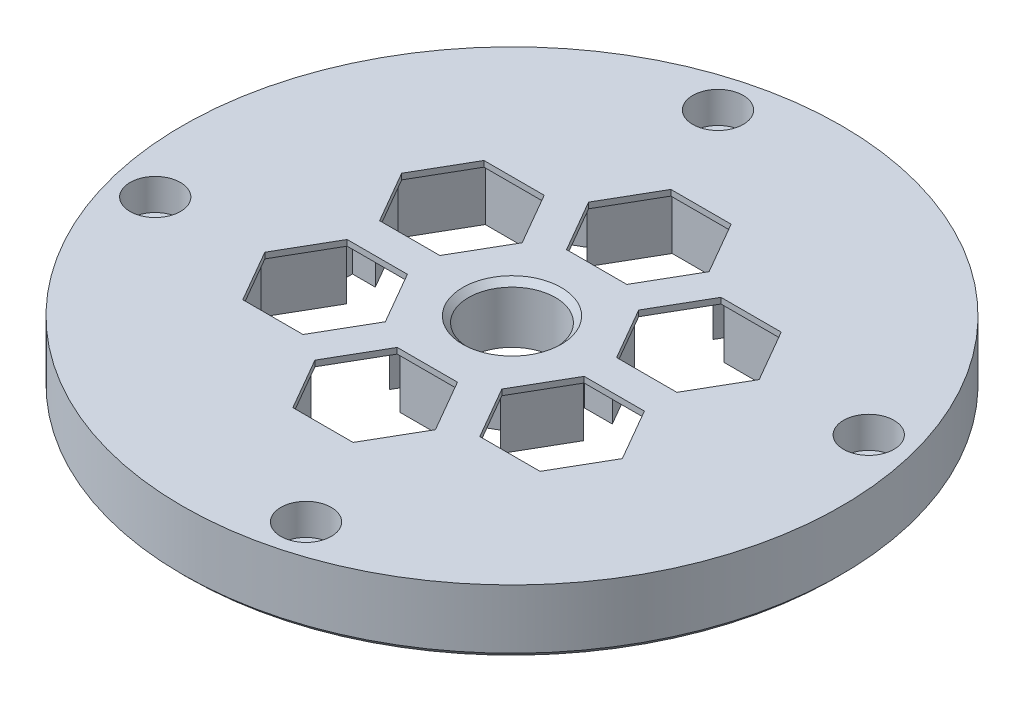
SolidWorks part; units mm, degrees
ref_plane "Front Plane" through (0, 0, 0) normal (0, 0, 1) x (1, 0, 0)
ref_plane "Top Plane" through (0, 0, 0) normal (0, 1, 0) x (1, 0, 0)
ref_plane "Right Plane" through (0, 0, 0) normal (1, 0, 0) x (0, 0, -1)
sketch "Sketch2" plane through (0, 0, 0) normal (0, 1, 0) x (1, 0, 0)
  circle A0 centre (0, 0) radius 44.5
  circle A1 centre (0, 0) radius 56.85
  dimension "D1" = 89
  dimension "D2" = 113.7
extrude "Boss-Extrude1" add sketch "Sketch2" along normal blind 1.2
sketch "Sketch3" plane through (0, 1.2, 0) normal (0, 1, 0) x (1, 0, 0)
  circle A0 centre (0, 0) radius 56.85
  dimension "D1" = 113.7
extrude "Boss-Extrude2" add sketch "Sketch3" along normal blind 10
sketch "Sketch4" plane through (0, 11.2, 0) normal (0, 1, 0) x (1, 0, 0)
  line L0 (0, 0) -> (0, 50.25) construction
  line L1 (-13.0057, 48.5378) -> (0, 0) construction
  circle A0 centre (0, 0) radius 50.25 construction
  circle A1 centre (-13.0057, 48.5378) radius 2.65
  circle A2 centre (48.5378, 13.0057) radius 2.65
  circle A3 centre (13.0057, -48.5378) radius 2.65
  circle A4 centre (-48.5378, -13.0057) radius 2.65
  point P14 (0, 0)
  dimension "D1" = 100.5
  dimension "D2" = 5.3
  dimension "D4" = 15
  dimension "D3" = 4
extrude "Cut-Extrude1" cut sketch "Sketch4" against normal through all
sketch "Sketch5" plane through (0, 11.2, 0) normal (0, 1, 0) x (1, 0, 0)
  circle A0 centre (0, 0) radius 7.5
  dimension "D1" = 15
extrude "Cut-Extrude2" cut sketch "Sketch5" against normal through all
sketch "Sketch6" plane through (0, 1.2, 0) normal (0, -1, 0) x (1, 0, 0)
  line L0 (0, 0) -> (0, 33.1406) construction
  line L1 (0, 0) -> (5.0107, 8.6789) construction
  line L2 (8.2583, 18.8368) -> (11.0111, 23.6047) construction
  line L3 (11.0111, 23.6047) -> (5.5055, 33.1406)
  line L4 (5.5055, 33.1406) -> (-5.5055, 33.1406)
  line L5 (-5.5055, 33.1406) -> (-11.0111, 23.6047)
  line L6 (-8.2583, 18.8368) -> (-5.5055, 14.0688) construction
  line L7 (-5.5055, 14.0688) -> (5.5055, 14.0688)
  line L8 (2.8457, 9.9289) -> (5.2359, 14.0688)
  line L9 (12.8457, 27.2494) -> (17.1758, 24.7494)
  line L10 (17.1758, 24.7494) -> (15.2064, 21.3382)
  line L11 (7.1758, 7.4289) -> (2.8457, 9.9289)
  line L12 (14.9367, 2.2665) -> (25.9478, 2.2665) construction
  line L13 (25.9478, 2.2665) -> (31.4534, 11.8024)
  line L14 (31.4534, 11.8024) -> (25.9478, 21.3382)
  line L15 (25.9478, 21.3382) -> (14.9367, 21.3382)
  line L16 (14.9367, 21.3382) -> (9.4312, 11.8024) construction
  line L17 (9.4312, 11.8024) -> (14.9367, 2.2665)
  line L18 (10.0215, -2.5) -> (10.0215, 2.5)
  line L19 (10.0215, 2.5) -> (14.8019, 2.5)
  line L20 (30.0215, 2.5) -> (30.0215, -2.5)
  line L21 (30.0215, -2.5) -> (26.0827, -2.5)
  line L22 (9.4312, -11.8024) -> (14.9367, -21.3382) construction
  line L23 (14.9367, -21.3382) -> (25.9478, -21.3382)
  line L24 (25.9478, -21.3382) -> (31.4534, -11.8024)
  line L25 (31.4534, -11.8024) -> (25.9478, -2.2665)
  line L26 (25.9478, -2.2665) -> (14.9367, -2.2665) construction
  line L27 (14.9367, -2.2665) -> (9.4312, -11.8024)
  line L28 (2.8457, -9.9289) -> (7.1758, -7.4289)
  line L29 (7.1758, -7.4289) -> (9.566, -11.5688)
  line L30 (17.1758, -24.7494) -> (12.8457, -27.2494)
  line L31 (12.8457, -27.2494) -> (10.8763, -23.8382)
  line L32 (-5.5055, -14.0688) -> (-11.0111, -23.6047) construction
  line L33 (-11.0111, -23.6047) -> (-5.5055, -33.1406)
  line L34 (-5.5055, -33.1406) -> (5.5055, -33.1406)
  line L35 (5.5055, -33.1406) -> (11.0111, -23.6047)
  line L36 (11.0111, -23.6047) -> (5.5055, -14.0688) construction
  line L37 (5.5055, -14.0688) -> (-5.5055, -14.0688)
  line L38 (-7.1758, -7.4289) -> (-2.8457, -9.9289)
  line L39 (-2.8457, -9.9289) -> (-5.2359, -14.0688)
  line L40 (-12.8457, -27.2494) -> (-17.1758, -24.7494)
  line L41 (-17.1758, -24.7494) -> (-15.2064, -21.3382)
  line L42 (-14.9367, -2.2665) -> (-25.9478, -2.2665) construction
  line L43 (-25.9478, -2.2665) -> (-31.4534, -11.8024)
  line L44 (-31.4534, -11.8024) -> (-25.9478, -21.3382)
  line L45 (-25.9478, -21.3382) -> (-14.9367, -21.3382)
  line L46 (-14.9367, -21.3382) -> (-9.4312, -11.8024) construction
  line L47 (-9.4312, -11.8024) -> (-14.9367, -2.2665)
  line L48 (-10.0215, 2.5) -> (-10.0215, -2.5)
  line L49 (-10.0215, -2.5) -> (-14.8019, -2.5)
  line L50 (-30.0215, -2.5) -> (-30.0215, 2.5)
  line L51 (-30.0215, 2.5) -> (-26.0827, 2.5)
  line L52 (-9.4312, 11.8024) -> (-14.9367, 21.3382) construction
  line L53 (-14.9367, 21.3382) -> (-25.9478, 21.3382)
  line L54 (-25.9478, 21.3382) -> (-31.4534, 11.8024)
  line L55 (-31.4534, 11.8024) -> (-25.9478, 2.2665)
  line L56 (-25.9478, 2.2665) -> (-14.9367, 2.2665) construction
  line L57 (-14.9367, 2.2665) -> (-9.4312, 11.8024)
  line L58 (-2.8457, 9.9289) -> (-7.1758, 7.4289)
  line L59 (-7.1758, 7.4289) -> (-9.566, 11.5688)
  line L60 (-17.1758, 24.7494) -> (-12.8457, 27.2494)
  line L61 (-12.8457, 27.2494) -> (-10.8763, 23.8382)
  line L62 (-9.1048, 20.77) -> (-7.0073, 17.1371) construction
  line L63 (-5.2359, 14.0688) -> (-2.8457, 9.9289)
  line L64 (-11.0111, 23.6047) -> (-8.2583, 18.8368) construction
  line L65 (-10.8763, 23.8382) -> (-9.1048, 20.77) construction
  line L66 (-9.566, 11.5688) -> (-15.2064, 21.3382) construction
  line L67 (-15.2064, 21.3382) -> (-17.1758, 24.7494)
  line L68 (-7.0073, 17.1371) -> (-5.2359, 14.0688) construction
  line L69 (5.2359, 14.0688) -> (7.0073, 17.1371) construction
  line L70 (7.0073, 17.1371) -> (9.1048, 20.77) construction
  line L71 (5.5055, 14.0688) -> (8.2583, 18.8368) construction
  line L72 (5.0107, 8.6789) -> (15.0107, 25.9994) construction
  line L73 (9.1048, 20.77) -> (10.8763, 23.8382) construction
  line L74 (10.8763, 23.8382) -> (12.8457, 27.2494)
  line L75 (15.2064, 21.3382) -> (9.566, 11.5688) construction
  line L76 (9.566, 11.5688) -> (7.1758, 7.4289)
  line L77 (14.8019, 2.5) -> (26.0827, 2.5) construction
  line L78 (26.0827, 2.5) -> (30.0215, 2.5)
  line L79 (26.0827, -2.5) -> (14.8019, -2.5) construction
  line L80 (14.8019, -2.5) -> (10.0215, -2.5)
  line L81 (9.566, -11.5688) -> (15.2064, -21.3382) construction
  line L82 (15.2064, -21.3382) -> (17.1758, -24.7494)
  line L83 (10.8763, -23.8382) -> (5.2359, -14.0688) construction
  line L84 (5.2359, -14.0688) -> (2.8457, -9.9289)
  line L85 (-5.2359, -14.0688) -> (-10.8763, -23.8382) construction
  line L86 (-10.8763, -23.8382) -> (-12.8457, -27.2494)
  line L87 (-15.2064, -21.3382) -> (-9.566, -11.5688) construction
  line L88 (-9.566, -11.5688) -> (-7.1758, -7.4289)
  line L89 (-14.8019, -2.5) -> (-26.0827, -2.5) construction
  line L90 (-26.0827, -2.5) -> (-30.0215, -2.5)
  line L91 (-26.0827, 2.5) -> (-14.8019, 2.5) construction
  line L92 (-14.8019, 2.5) -> (-10.0215, 2.5)
  arc A0 (-8.2583, 18.8368) -> (-7.0073, 17.1371) centre (0, 23.6047) ccw construction
  arc A1 (-9.1048, 20.77) -> (-8.2583, 18.8368) centre (0, 23.6047) ccw construction
  arc A2 (-8.2583, 28.3727) -> (-9.1048, 20.77) centre (0, 23.6047) ccw construction
  arc A3 (-7.0073, 17.1371) -> (0, 14.0688) centre (0, 23.6047) ccw construction
  arc A4 (8.2583, 18.8368) -> (9.1048, 20.77) centre (0, 23.6047) ccw construction
  arc A5 (0, 14.0688) -> (7.0073, 17.1371) centre (0, 23.6047) ccw construction
  arc A6 (9.1048, 20.77) -> (8.2583, 28.3727) centre (0, 23.6047) ccw construction
  arc A7 (8.2583, 28.3727) -> (-8.2583, 28.3727) centre (0, 23.6047) ccw construction
  arc A8 (7.0073, 17.1371) -> (8.2583, 18.8368) centre (0, 23.6047) ccw construction
  point P4 (0, 33.1406)
  point P20 (5.0107, 8.6789)
  point P71 (0, 0)
  dimension "D2" = 19.0718
  dimension "D1" = 33.1406
  dimension "D3" = 30.0215
  dimension "D4" = 30
  dimension "D5" = 5
  dimension "D6" = 20
  dimension "D7" = 6
extrude "Cut-Extrude4" cut sketch "Sketch6" against normal through all
sketch "Sketch7" plane through (0, 11.2, 0) normal (0, 1, 0) x (1, 0, 0)
  line L0 (-17.1758, 24.7494) -> (-7.1758, 7.4289)
  line L1 (-7.1758, 7.4289) -> (-2.8457, 9.9289)
  line L2 (-2.8457, 9.9289) -> (-12.8457, 27.2494)
  line L3 (-12.8457, 27.2494) -> (-17.1758, 24.7494)
  line L4 (17.1758, 24.7494) -> (12.8457, 27.2494)
  line L5 (12.8457, 27.2494) -> (2.8457, 9.9289)
  line L6 (2.8457, 9.9289) -> (7.1758, 7.4289)
  line L7 (7.1758, 7.4289) -> (17.1758, 24.7494)
  line L8 (30.0215, -2.5) -> (30.0215, 2.5)
  line L9 (30.0215, 2.5) -> (10.0215, 2.5)
  line L10 (10.0215, 2.5) -> (10.0215, -2.5)
  line L11 (10.0215, -2.5) -> (30.0215, -2.5)
  line L12 (12.8457, -27.2494) -> (17.1758, -24.7494)
  line L13 (17.1758, -24.7494) -> (7.1758, -7.4289)
  line L14 (7.1758, -7.4289) -> (2.8457, -9.9289)
  line L15 (2.8457, -9.9289) -> (12.8457, -27.2494)
  line L16 (-17.1758, -24.7494) -> (-12.8457, -27.2494)
  line L17 (-12.8457, -27.2494) -> (-2.8457, -9.9289)
  line L18 (-2.8457, -9.9289) -> (-7.1758, -7.4289)
  line L19 (-7.1758, -7.4289) -> (-17.1758, -24.7494)
  line L20 (-30.0215, 2.5) -> (-30.0215, -2.5)
  line L21 (-30.0215, -2.5) -> (-10.0215, -2.5)
  line L22 (-10.0215, -2.5) -> (-10.0215, 2.5)
  line L23 (-10.0215, 2.5) -> (-30.0215, 2.5)
  point P31 (0, 0)
  dimension "D1" = 6
extrude "Boss-Extrude3" add sketch "Sketch7" against normal blind 1
sketch "Sketch8" plane through (0, 11.2, 0) normal (0, 1, 0) x (1, 0, 0)
  line L0 (0, 0) -> (0, -23.6047) construction
  line L9 (5.5426, -14.0047) -> (-5.5426, -14.0047)
  line L10 (-5.5426, -14.0047) -> (-11.0851, -23.6047)
  line L11 (-11.0851, -23.6047) -> (-5.5426, -33.2047)
  line L12 (-5.5426, -33.2047) -> (5.5426, -33.2047)
  line L13 (5.5426, -33.2047) -> (11.0851, -23.6047)
  line L14 (11.0851, -23.6047) -> (5.5426, -14.0047)
  line L15 (5.1962, -14.6047) -> (-5.1962, -14.6047)
  line L16 (-5.1962, -14.6047) -> (-10.3923, -23.6047)
  line L17 (-10.3923, -23.6047) -> (-5.1962, -32.6047)
  line L18 (-5.1962, -32.6047) -> (5.1962, -32.6047)
  line L19 (5.1962, -32.6047) -> (10.3923, -23.6047)
  line L20 (10.3923, -23.6047) -> (5.1962, -14.6047)
  circle A0 centre (0, -23.6047) radius 9.6 construction
  circle A1 centre (0, -23.6047) radius 9 construction
  point P63 (0, 0)
  dimension "D2" = 19.2
  dimension "D3" = 18
  dimension "D1" = 23.6047
extrude "Boss-Extrude4" add sketch "Sketch8" against normal blind 1
pattern_circular "CirPattern1" count 6 over 360 about axis through (0, 0, 0) along (0, 1, 0) of "Boss-Extrude4"
sketch "Sketch9" plane through (0, 11.2, 0) normal (0, 1, 0) x (1, 0, 0)
  circle A0 centre (-13.0057, 48.5378) radius 4.35
  circle A1 centre (48.5378, 13.0057) radius 4.35
  circle A2 centre (13.0057, -48.5378) radius 4.35
  circle A3 centre (-48.5378, -13.0057) radius 4.35
  point P12 (0, 0)
  dimension "D1" = 8.7
  dimension "D2" = 4
extrude "Cut-Extrude5" cut sketch "Sketch9" against normal blind 5.4
chamfer "Chamfer1" distance 1 angle 45 2 edges at (0, 0, 44.5) (0, 0, 56.85)
chamfer "Chamfer2" distance 1 angle 45 1 edges at (0, 11.2, 7.5)
